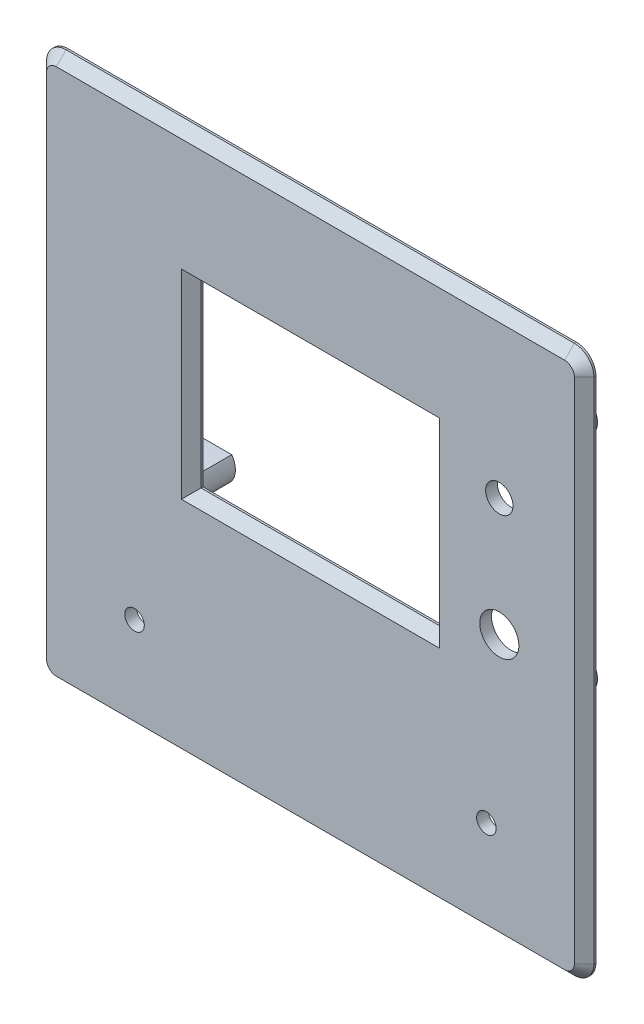
SolidWorks part; units mm, degrees
ref_plane "Front Plane" through (0, 0, 0) normal (0, 0, 1) x (1, 0, 0)
ref_plane "Top Plane" through (0, 0, 0) normal (0, 1, 0) x (1, 0, 0)
ref_plane "Right Plane" through (0, 0, 0) normal (1, 0, 0) x (0, 0, -1)
sketch "Sketch1" plane through (0, 0, 0) normal (0, 0, 1) x (1, 0, 0)
  line L1 (-30.5, -23) -> (30.5, -23)
  line L2 (-30.5, -23) -> (-30.5, 23)
  line L3 (-30.5, 23) -> (30.5, 23)
  line L4 (30.5, -23) -> (30.5, 23)
  line L5 (-30.5, -23) -> (30.5, 23) construction
  line L6 (-30.5, 23) -> (30.5, -23) construction
  line L7 (-70, -83.1992) -> (70, -83.1992)
  line L8 (-70, -83.1992) -> (-70, 56.8008)
  line L9 (-70, 56.8008) -> (70, 56.8008)
  line L10 (70, -83.1992) -> (70, 56.8008)
  line L11 (-70, -83.1992) -> (70, 56.8008) construction
  line L12 (-70, 56.8008) -> (70, -83.1992) construction
  circle A0 centre (48.3, 15.4) radius 3.5
  circle A1 centre (-40.5, 28.4) radius 2
  circle A2 centre (52.1, 28.4) radius 2
  circle A3 centre (52.1, -28.4) radius 2
  circle A4 centre (-40.5, -28.4) radius 2
  circle A5 centre (48.3, -14.8) radius 5
  circle A6 centre (45, -58.1992) radius 2.5
  circle A7 centre (-45, -58.1992) radius 2.5
  point P0 (0, 0)
  point P18 (0, -13.1992)
  dimension "D6" = 4
  dimension "D8" = 7
  dimension "D9" = 10
  dimension "D15" = 5
  dimension "D1" = 61
  dimension "D2" = 46
  dimension "D3" = 92.6
  dimension "D4" = 56.8
  dimension "D7" = 30.2
  dimension "D10" = 28.4
  dimension "D11" = 3.8
  dimension "D12" = 13
  dimension "D5" = 10
  dimension "D13" = 140
  dimension "D14" = 140
  dimension "D16" = 25
  dimension "D17" = 25
  dimension "D18" = 25
extrude "Boss-Extrude1" add sketch "Sketch1" along normal blind 3
chamfer "Chamfer1" distance 2.5 angle 45 4 edges at (-30.5, 0, 3) (0, 23, 3) (30.5, 0, 3) (0, -23, 3)
fillet "Fillet1" radius 5 4 edges at (-70, 56.8008, 1.5) (70, 56.8008, 1.5) (70, -83.1992, 1.5) (-70, -83.1992, 1.5)
chamfer "Chamfer2" distance 2.5 angle 45 8 edges at (0, -83.1992, 3) (68.5355, -81.7348, 3) (-68.5355, -81.7348, 3) (70, -13.1992, 3) (-70, -13.1992, 3) (68.5355, 55.3363, 3) (-68.5355, 55.3363, 3) (0, 56.8008, 3)
sketch "Sketch2" plane through (0, 0, 0) normal (0, 0, 1) x (1, 0, 0)
  circle A0 centre (52.1, 28.4) radius 5
  circle A1 centre (52.1, -28.4) radius 5
  circle A2 centre (-40.5, 28.4) radius 5
  circle A3 centre (-40.5, -28.4) radius 5
  dimension "D1" = 10
extrude "Boss-Extrude3" add sketch "Sketch2" against normal blind 13.3
chamfer "Chamfer3" distance 3 angle 45 4 edges at (47.1, -28.4, 0) (-45.5, -28.4, 0) (-45.5, 28.4, 0) (47.1, 28.4, 0)
sketch "Sketch4" plane through (0, 0, -13.3) normal (0, 0, -1) x (-1, 0, 0)
  circle A0 centre (-52.1, 28.4) radius 2
  circle A1 centre (40.5, 28.4) radius 2
  circle A2 centre (40.5, -28.4) radius 2
  circle A3 centre (-52.1, -28.4) radius 2
  dimension "D1" = 4
extrude "Cut-Extrude1" cut sketch "Sketch4" against normal blind 8
sketch "Sketch6" plane through (0, 0, -13.3) normal (0, 0, -1) x (-1, 0, 0)
  line L0 (70, 51.8008) -> (70, -78.1992) construction
  line L1 (-19.5833, -25.5) -> (70, -25.5)
  line L2 (-19.5833, -25.5) -> (-19.5833, 25.5)
  line L3 (-19.5833, 25.5) -> (70, 25.5)
  line L4 (70, -25.5) -> (70, 25.5)
  line L5 (-19.5833, -25.5) -> (70, 25.5) construction
  line L6 (-19.5833, 25.5) -> (70, -25.5) construction
  point P0 (25.2084, 0)
  dimension "D1" = 51
extrude "Cut-Extrude2" cut sketch "Sketch6" against normal blind 13.3
sketch "Sketch7" plane through (0, 0, 3) normal (0, 0, 1) x (1, 0, 0)
  circle A0 centre (-40.5, 28.4) radius 4.2745
  circle A1 centre (-40.5, -28.4) radius 4.2884
  circle A2 centre (52.1, 28.4) radius 5.4064
  circle A3 centre (52.1, -28.4) radius 4.246
extrude "Boss-Extrude4" add sketch "Sketch7" against normal blind 3
equation "\"D10@Sketch1\"=\"D4@Sketch1\"/2"
